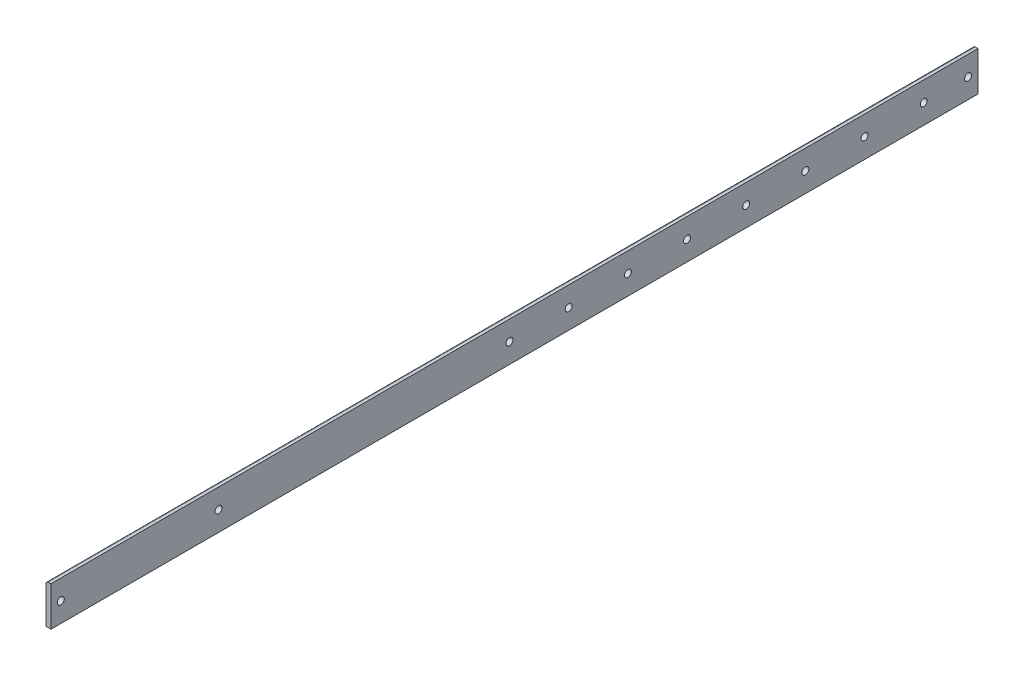
SolidWorks part; units mm, degrees
ref_plane "Front Plane" through (0, 0, 0) normal (0, 0, 1) x (1, 0, 0)
ref_plane "Top Plane" through (0, 0, 0) normal (0, 1, 0) x (1, 0, 0)
ref_plane "Right Plane" through (0, 0, 0) normal (1, 0, 0) x (0, 0, -1)
sketch "Sketch0" plane through (0, 0, 0) normal (0, 0, 1) x (1, 0, 0)
  line L0 (-12.7, -12.7) -> (12.7, -12.7)
  line L1 (12.7, -12.7) -> (12.7, 12.7)
  line L2 (12.7, 0) -> (0, 0) construction
  line L3 (0, 0) -> (0, -12.7) construction
  line L4 (9.525, -6.35) -> (9.525, 12.7) construction
  line L5 (6.35, -9.525) -> (-12.7, -9.525) construction
  arc A0 (9.525, -6.35) -> (6.35, -9.525) centre (6.35, -6.35) cw
  point P3 (8.5951, -8.5951)
  dimension "Inside Corner Radius" = 3.175
  dimension "Outside Height" = 25.4
  dimension "Inside Height" = 22.225
  dimension "Inside Width" = 22.225
  dimension "Wall Thickness" = 3.175
  dimension "D1" = 3.175
  dimension "Outside Width" = 25.4
sketch "Sketch1" plane through (0, 0, 0) normal (1, 0, 0) x (0, 0, -1)
  line L0 (304.8, 0) -> (-304.8, 0)
  point P4 (0, 0)
  dimension "Length" = 609.6
sketch "Sketch2" plane through (0, 0, 0) normal (0, 0, 1) x (1, 0, 0)
  line L0 (-12.7, -12.7) -> (12.7, -12.7)
  line L1 (12.7, -12.7) -> (12.7, 12.7)
  line L2 (12.7, 12.7) -> (9.525, 12.7) construction
  line L3 (9.525, 11.1125) -> (9.525, -6.35)
  line L4 (6.35, -9.525) -> (-11.1125, -9.525)
  line L5 (-12.7, -12.7) -> (-12.7, -9.525) construction
  line L6 (11.1125, 12.7) -> (12.7, 12.7)
  line L7 (-12.7, -11.1125) -> (-12.7, -12.7)
  line L8 (12.7, 0) -> (0, 0) construction
  line L9 (0, 0) -> (0, -12.7) construction
  arc A0 (9.525, 11.1125) -> (11.1125, 12.7) centre (11.1125, 11.1125) cw
  arc A1 (-12.7, -11.1125) -> (-11.1125, -9.525) centre (-11.1125, -11.1125) cw
  arc A2 (9.525, -6.35) -> (6.35, -9.525) centre (6.35, -6.35) cw
  dimension "Inside Radius" = 3.175
  dimension "Height" = 25.4
  dimension "Width" = 25.4
  dimension "Thickness" = 3.175
extrude "Boss-Extrude1" add sketch "Sketch2" along normal mid plane 609.6
sketch "Break Locations" plane through (0, 0, 0) normal (1, 0, 0) x (0, 0, -1)
  line L0 (-278.892, 0) -> (278.892, 0)
  line L1 (-304.8, -12.7) -> (-304.8, 12.7) construction
  line L2 (304.8, -12.7) -> (304.8, 12.7) construction
  point P0 (-283.21, 0)
  point P1 (283.21, 0)
  point P10 (0, 0)
  point P11 (278.892, 0)
  point P13 (-278.892, 0)
  dimension "D1" = 21.59
  dimension "D2" = 21.59
  dimension "D3" = 25.908
sketch "Sketch7" plane through (0, -12.7, 0) normal (0, -1, 0) x (1, 0, 0)
  line L0 (-12.7, 292.1) -> (12.7, 292.1)
  line L1 (-12.7, 304.8) -> (12.7, 304.8)
  line L2 (-12.7, 304.8) -> (-12.7, -304.8)
  line L3 (-12.7, -304.8) -> (12.7, -304.8)
  line L4 (12.7, 304.8) -> (12.7, -304.8)
  line M4 (12.7, -304.8) -> (12.7, 304.8)
  line M5 (12.7, 304.8) -> (-12.7, 304.8)
  line M6 (-12.7, 304.8) -> (-12.7, -304.8)
  dimension "D1" = 596.9
extrude "Cut-Extrude1" cut sketch "Sketch7" against normal blind 254 contours L0 M6 M4 M5
sketch "Sketch3" plane through (0, 0, 0) normal (0, 1, 0) x (1, 0, 0)
  line L2 (12.7, -292.1) -> (12.7, 304.8) construction
  line L3 (6.35, 304.8) -> (-11.1125, 304.8) construction
  line L4 (-11.1125, 6.35) -> (6.35, 6.35) construction
  line L5 (-11.1125, -292.1) -> (-11.1125, 304.8) construction
  line L6 (6.35, -292.1) -> (6.35, 304.8) construction
  line L7 (0, 273.05) -> (0, 234.95) construction
  circle A2 centre (0, 273.05) radius 2.5
  circle A3 centre (0, 234.95) radius 2.5
  circle A4 centre (0, 196.85) radius 2.5
  circle A5 centre (0, 158.75) radius 2.5
  circle A6 centre (0, 120.65) radius 2.5
  circle A7 centre (0, 82.55) radius 2.5
  circle A8 centre (0, 44.45) radius 2.5
  circle A9 centre (0, 6.35) radius 2.5
  circle A10 centre (0, -31.75) radius 2.5
  circle A11 centre (0, -69.85) radius 2.5
  circle A12 centre (0, -107.95) radius 2.5
  dimension "D1" = 5
  dimension "D6" = 12.7
  dimension "D7" = 31.75
  dimension "D9" = 38.1
  dimension "D8" = 11
extrude "Cut-Extrude2" cut sketch "Sketch3" against normal blind 254
sketch "Sketch8" plane through (12.7, 0, -12.7) normal (-1, 0, 0) x (0, 0, 1)
  line L0 (304.8, -6.35) -> (-292.1, -6.35) construction
  line L1 (304.8, 11.1125) -> (-292.1, 11.1125) construction
  line L2 (304.8, -12.7) -> (-292.1, -12.7) construction
  line L3 (-292.1, 11.1125) -> (-292.1, -6.35) construction
  line L4 (6.35, 11.1125) -> (6.35, -6.35) construction
  line L5 (-142.875, 0) -> (-104.775, 0) construction
  line L6 (304.8, -6.35) -> (304.8, 11.1125) construction
  line L7 (9.525, 0) -> (-28.575, 0) construction
  circle A2 centre (9.525, 0) radius 2.25
  circle A3 centre (-28.575, 0) radius 2.25
  circle A4 centre (-66.675, 0) radius 2.25
  circle A5 centre (-104.775, 0) radius 2.25
  circle A6 centre (-142.875, 0) radius 2.25
  circle A7 centre (-180.975, 0) radius 2.25
  circle A8 centre (-219.075, 0) radius 2.25
  circle A13 centre (-285.75, 0) radius 2.25
  circle A14 centre (-257.175, 0) radius 2.25
  circle A15 centre (298.45, 0) radius 2.25
  point P0 (-123.825, 0)
  dimension "D3" = 6.35
  dimension "D1" = 4.5
  dimension "D2" = 12.7
  dimension "D4" = 6.35
  dimension "D5" = 34.925
  dimension "D9" = 38.1
  dimension "D8" = 8
extrude "Cut-Extrude4" cut sketch "Sketch8" along normal blind 254
sketch "Sketch9" plane through (0, -9.525, 0) normal (0, 1, 0) x (1, 0, 0)
  line L0 (9.525, -292.1) -> (9.525, 304.8) construction
  line L1 (9.525, -292.1) -> (9.525, 304.8) construction
  line L2 (-12.7, -292.1) -> (-12.7, 304.8) construction
  line L3 (-12.7, -292.1) -> (-12.7, 304.8) construction
  line L4 (6.35, 304.8) -> (-11.1125, 304.8) construction
  line L5 (-12.7, 304.8) -> (9.525, 304.8)
  line L6 (-12.7, 304.8) -> (-12.7, 273.05)
  line L7 (-12.7, 273.05) -> (9.525, 273.05)
  line L8 (9.525, 304.8) -> (9.525, 273.05)
  line L9 (-12.7, -292.1) -> (9.525, -292.1)
  line L10 (-12.7, -292.1) -> (-12.7, -260.35)
  line L11 (-12.7, -260.35) -> (9.525, -260.35)
  line L12 (9.525, -292.1) -> (9.525, -260.35)
  line L13 (-12.7, -19.05) -> (9.525, -19.05)
  line L14 (-12.7, -19.05) -> (-12.7, -50.8)
  line L15 (-12.7, -50.8) -> (9.525, -50.8)
  line L16 (9.525, -19.05) -> (9.525, -50.8)
  line L17 (-12.7, -165.1) -> (9.525, -165.1)
  line L18 (-12.7, -165.1) -> (-12.7, -196.85)
  line L19 (-12.7, -196.85) -> (9.525, -196.85)
  line L20 (9.525, -165.1) -> (9.525, -196.85)
  dimension "D1" = 31.75
  dimension "D2" = 355.6
  dimension "D3" = 469.9
extrude "Cut-Extrude5" cut sketch "Sketch9" against normal blind 12.7 and the other way blind 12.7
sketch "Sketch10" plane through (12.7, 0, 0) normal (1, 0, 0) x (0, 0, -1)
  circle A0 centre (-184.15, 0) radius 2.25
  circle A1 centre (-285.75, 0) radius 2.25 construction
  circle A2 centre (-285.75, 0) radius 2.25
  point P4 (0, 0)
  point P6 (0, 0)
  dimension "D1" = 101.6
extrude "Cut-Extrude6" cut sketch "Sketch10" against normal blind 203.2
equation "\"D1@Break Locations\" = .85 * \"Height@Sketch2\""
equation "\"D2@Break Locations\"=\"D1@Break Locations\""
equation "\"Thickness@Sketch2\" = \"Wall Thickness@Sketch0\""
equation "\"Height@Sketch2\" = \"Outside Height@Sketch0\""
equation "\"Width@Sketch2\" = \"Outside Width@Sketch0\""
equation "\"Inside Radius@Sketch2\" = \"Inside Corner Radius@Sketch0\""
equation "\"Length@Boss-Extrude1\" = \"Length@Sketch1\""
equation "\"D3@Break Locations\"=\"D2@Break Locations\"*1.2"
equation "\"D1@Sketch0\"=\"Wall Thickness@Sketch0\""
